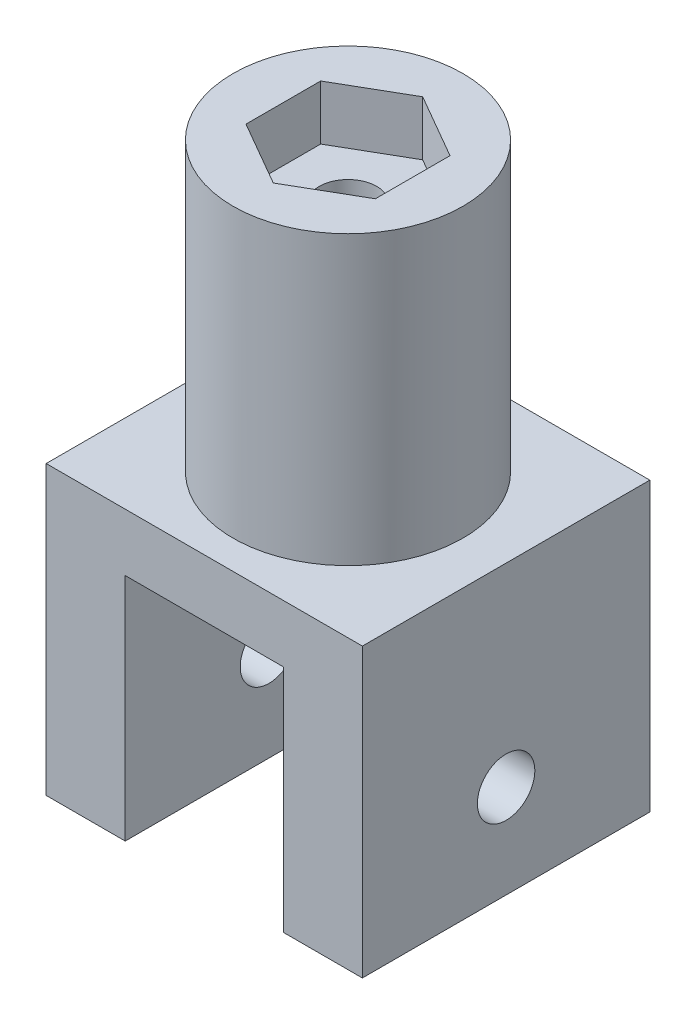
SolidWorks part; units mm, degrees
ref_plane "Front Plane" through (0, 0, 0) normal (0, 0, 1) x (1, 0, 0)
ref_plane "Top Plane" through (0, 0, 0) normal (0, 1, 0) x (1, 0, 0)
ref_plane "Right Plane" through (0, 0, 0) normal (1, 0, 0) x (0, 0, -1)
sketch "Sketch1" plane through (0, 0, 0) normal (0, 1, 0) x (1, 0, 0)
  circle A0 centre (0, 0) radius 6.5
  circle A2 centre (0, 0) radius 2
  dimension "D1" = 13
  dimension "D2" = 4
extrude "Boss-Extrude1" add sketch "Sketch1" along normal blind 20
sketch "Sketch6" plane through (0, 0, 0) normal (0, -1, 0) x (1, 0, 0)
  line L0 (0, 0) -> (11, 0) construction
  line L5 (0, 0) -> (-11, 0) construction
  line L6 (0, 0) -> (0, 10) construction
  line L7 (0, 0) -> (0, -10) construction
  line L9 (-11, 10) -> (-11, -10)
  line L10 (-11, -10) -> (11, -10)
  line L11 (11, -10) -> (11, 10)
  line L13 (-11, 10) -> (11, 10)
  dimension "D1" = 20
  dimension "D2" = 22
extrude "Boss-Extrude2" add sketch "Sketch6" along normal blind 4
sketch "Sketch7" plane through (0, 0, 10) normal (0, 0, 1) x (1, 0, 0)
  line L0 (-11, -4) -> (-11, 0) construction
  line L1 (11, 0) -> (5.5, 0)
  line L2 (11, 0) -> (11, -20)
  line L3 (11, -20) -> (5.5, -20)
  line L4 (5.5, 0) -> (5.5, -20)
  line L5 (-11, 0) -> (-5.5, 0)
  line L6 (-11, 0) -> (-11, -20)
  line L7 (-11, -20) -> (-5.5, -20)
  line L8 (-5.5, 0) -> (-5.5, -20)
  line L9 (11, 0) -> (-11, 0) construction
  dimension "D1" = 11
  dimension "D2" = 20
extrude "Boss-Extrude3" add sketch "Sketch7" against normal up to surface (20 mm away) up to face at (0, -2, -10)
sketch "Sketch8" plane through (11, 0, 0) normal (1, 0, 0) x (0, 0, -1)
  line L0 (10, -13.5) -> (-10, -13.5) construction
  line L1 (10, -20) -> (10, 0) construction
  line L2 (-10, -20) -> (-10, 0) construction
  line L3 (10, -20) -> (-10, -20) construction
  circle A0 centre (0, -13.5) radius 2
  dimension "D2" = 4
  dimension "D1" = 6.5
extrude "Cut-Extrude1" cut sketch "Sketch8" against normal through all
sketch "Sketch14" plane through (0, 0, 0) normal (0, 1, 0) x (1, 0, 0)
  circle A0 centre (0, 0) radius 8
  circle A1 centre (0, 0) radius 6.5
  dimension "D1" = 16
  dimension "D2" = 13
extrude "Boss-Extrude4" add sketch "Sketch14" along normal up to surface (20 mm away) up to face at (0, 20, 6.5)
sketch "Sketch15" plane through (0, 20, 0) normal (0, 1, 0) x (1, 0, 0)
  line L0 (0, 8) -> (0, -8) construction
  line L1 (-8, 0) -> (8, 0) construction
  line L3 (4.5, 2.5981) -> (0, 5.1962)
  line L4 (0, 5.1962) -> (-4.5, 2.5981)
  line L5 (-4.5, 2.5981) -> (-4.5, -2.5981)
  line L6 (-4.5, -2.5981) -> (0, -5.1962)
  line L7 (0, -5.1962) -> (4.5, -2.5981)
  line L8 (4.5, -2.5981) -> (4.5, 2.5981)
  circle A0 centre (0, 0) radius 8 construction
  circle A1 centre (0, 0) radius 4.5 construction
  dimension "D1" = 9
extrude "Cut-Extrude2" cut sketch "Sketch15" against normal blind 3.8
sketch "Sketch16" plane through (0, 0, 0) normal (0, 1, 0) x (1, 0, 0)
  circle A0 centre (0, 0) radius 2
  circle A1 centre (0, 0) radius 2 construction
extrude "Cut-Extrude3" cut sketch "Sketch16" against normal through all
